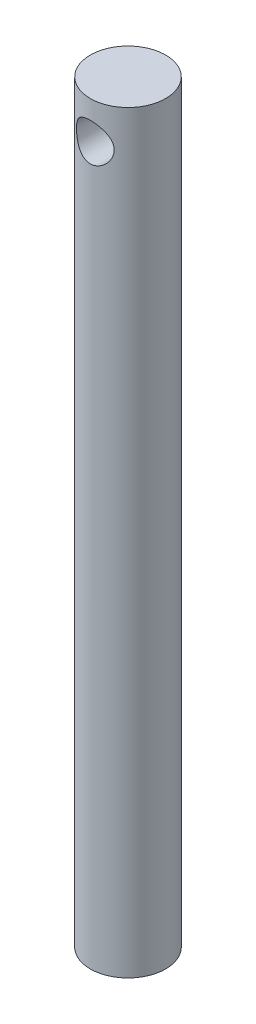
SolidWorks part; units mm, degrees
ref_plane "Спереди" through (0, 0, 0) normal (0, 0, 1) x (1, 0, 0)
ref_plane "Сверху" through (0, 0, 0) normal (0, 1, 0) x (1, 0, 0)
ref_plane "Справа" through (0, 0, 0) normal (1, 0, 0) x (0, 0, -1)
sketch "Эскиз1" plane through (0, 0, 0) normal (0, 1, 0) x (1, 0, 0)
  circle A0 centre (0, 0) radius 5
  dimension "D1" = 10
extrude "Бобышка-Вытянуть1" add sketch "Эскиз1" along normal blind 100 contours A0
sketch "Эскиз2" plane through (0, 0, 0) normal (0, 0, 1) x (1, 0, 0)
  line L0 (0, 100) -> (0, 0) construction
  line L1 (5, 100) -> (-5, 100) construction
  circle A0 centre (0, 95) radius 2.5
  dimension "D1" = 5
  dimension "D2" = 5
extrude "Вырез-Вытянуть1" cut sketch "Эскиз2" against normal blind 8 and the other way blind 10 contours A0
